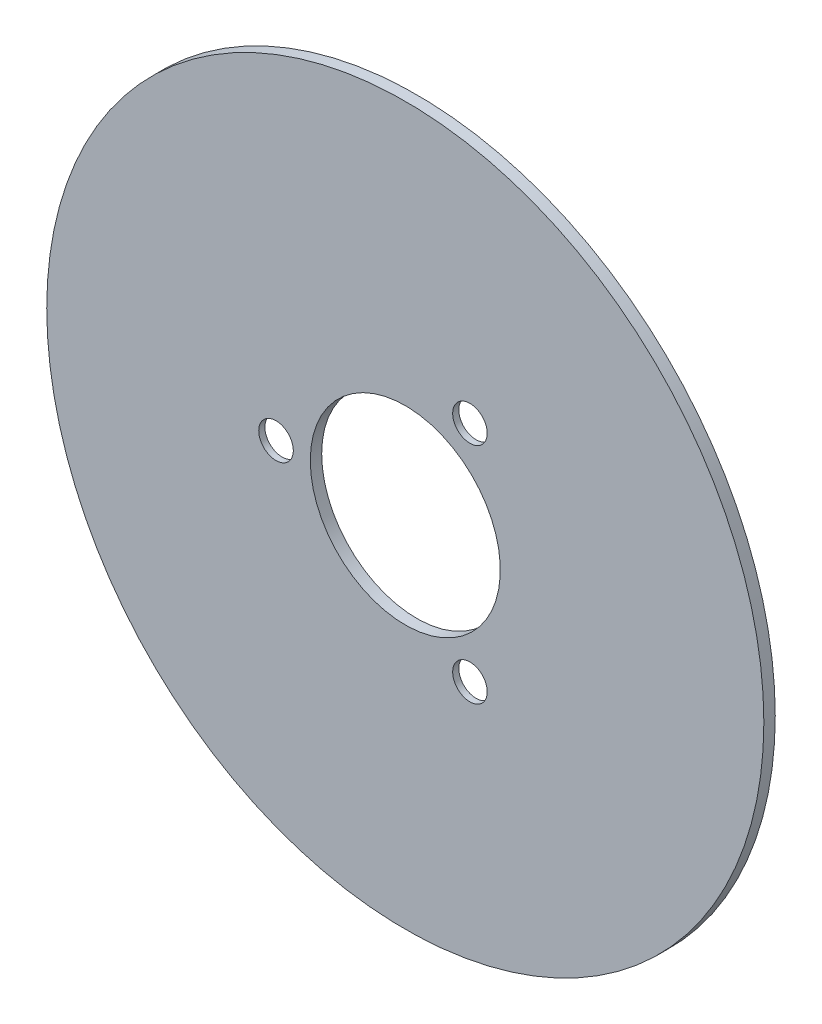
SolidWorks part; units mm, degrees
ref_plane "Front Plane" through (0, 0, 0) normal (0, 0, 1) x (1, 0, 0)
ref_plane "Top Plane" through (0, 0, 0) normal (0, 1, 0) x (1, 0, 0)
ref_plane "Right Plane" through (0, 0, 0) normal (1, 0, 0) x (0, 0, -1)
sketch "Sketch1" plane through (0, 0, 0) normal (0, 0, 1) x (1, 0, 0)
  circle A0 centre (0, 0) radius 110
extrude "Boss-Extrude1" add sketch "Sketch1" along normal blind 3.5
sketch "Sketch2" plane through (0, 0, 0) normal (0, 0, -1) x (-1, 0, 0)
  circle A0 centre (0, 0) radius 80
extrude "Boss-Extrude2" add sketch "Sketch2" against normal blind 0.001
sketch "Sketch3" plane through (0, 0, 0) normal (0, 0, -1) x (-1, 0, 0)
  circle A0 centre (0, 0) radius 29.15
extrude "Cut-Extrude1" cut sketch "Sketch3" against normal through all
sketch "Sketch4" plane through (0, 0, 0) normal (0, 0, -1) x (-1, 0, 0)
  circle A0 centre (0, 0) radius 50.175
sketch "Sketch6" plane through (0, 0, 0) normal (0, 0, -1) x (-1, 0, 0)
  line L0 (0, 0) -> (-19.8313, 34.3487) construction
  line L1 (0, 0) -> (-19.8313, -34.3487) construction
  line L2 (0, 0) -> (39.6625, 0) construction
  circle A4 centre (39.6625, 0) radius 5.3
  circle A5 centre (39.6625, 0) radius 8.55
  circle A8 centre (-19.8313, -34.3487) radius 5.3
  circle A9 centre (-19.8313, -34.3487) radius 8.55
  circle A10 centre (-19.8313, 34.3487) radius 5.3
  circle A11 centre (-19.8313, 34.3487) radius 8.55
extrude "Cut-Extrude3" cut sketch "Sketch6" against normal blind 1.62
sketch "Sketch7" plane through (0, 0, 0) normal (0, 0, -1) x (-1, 0, 0)
  circle A0 centre (-19.8313, -34.3487) radius 5.3
  circle A1 centre (39.6625, 0) radius 5.3
  circle A2 centre (-19.8313, 34.3487) radius 5.3
extrude "Cut-Extrude4" cut sketch "Sketch7" against normal through all
sketch "Sketch8" plane through (0, 0, 0) normal (0, 0, -1) x (-1, 0, 0)
  circle A0 centre (0, 0) radius 80
extrude "Cut-Extrude5" cut sketch "Sketch8" against normal blind 0.001 contours A0
